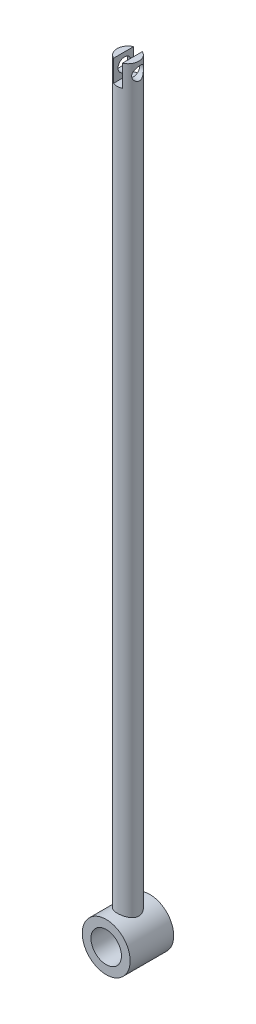
SolidWorks part; units mm, degrees
ref_plane "Front Plane" through (0, 0, 0) normal (0, 0, 1) x (1, 0, 0)
ref_plane "Top Plane" through (0, 0, 0) normal (0, 1, 0) x (1, 0, 0)
ref_plane "Right Plane" through (0, 0, 0) normal (1, 0, 0) x (0, 0, -1)
sketch "Sketch1" plane through (0, 0, 0) normal (0, 0, 1) x (1, 0, 0)
  circle A0 centre (0, 0) radius 3.5
  circle A1 centre (0, 0) radius 5.5
  dimension "D1" = 7
  dimension "D2" = 11
extrude "Boss-Extrude1" add sketch "Sketch1" along normal blind 10
sketch "Sketch2" plane through (0, 0, 0) normal (0, 1, 0) x (1, 0, 0)
  line L0 (5.5, 0) -> (-5.5, 0) construction
  circle A0 centre (0, -5) radius 2.5
  dimension "D2" = 5
  dimension "D1" = 5
extrude "Boss-Extrude2" add sketch "Sketch2" along normal blind 170
sketch "Sketch3" plane through (0, 0, 10) normal (0, 0, 1) x (1, 0, 0)
  circle A0 centre (0, 0) radius 3.5
extrude "Cut-Extrude1" cut sketch "Sketch3" against normal through all
sketch "Sketch4" plane through (0, 170, 0) normal (0, 1, 0) x (1, 0, 0)
  line L2 (1, -7.2913) -> (1, -2.7087)
  line L4 (-1, -7.2913) -> (-1, -2.7087)
  arc A0 (1, -7.2913) -> (1, -2.7087) centre (0, -5) ccw
  arc A1 (-1, -2.7087) -> (-1, -7.2913) centre (0, -5) ccw
  point P0 (0, -5)
extrude "Boss-Extrude3" add sketch "Sketch4" along normal blind 5
sketch "Sketch5" plane through (-1, 0, 0) normal (1, 0, 0) x (0, 0, -1)
  line L0 (-7.2913, 175) -> (-7.2913, 170) construction
  line L1 (-7.2913, 175) -> (-2.7087, 175) construction
  circle A0 centre (-4.7913, 172.5) radius 1.5
  point P6 (-4.6655, 173.3742)
  dimension "D1" = 3
  dimension "D2" = 2.5
  dimension "D3" = 2.5
extrude "Cut-Extrude2" cut sketch "Sketch5" against normal blind 5 and the other way through all
